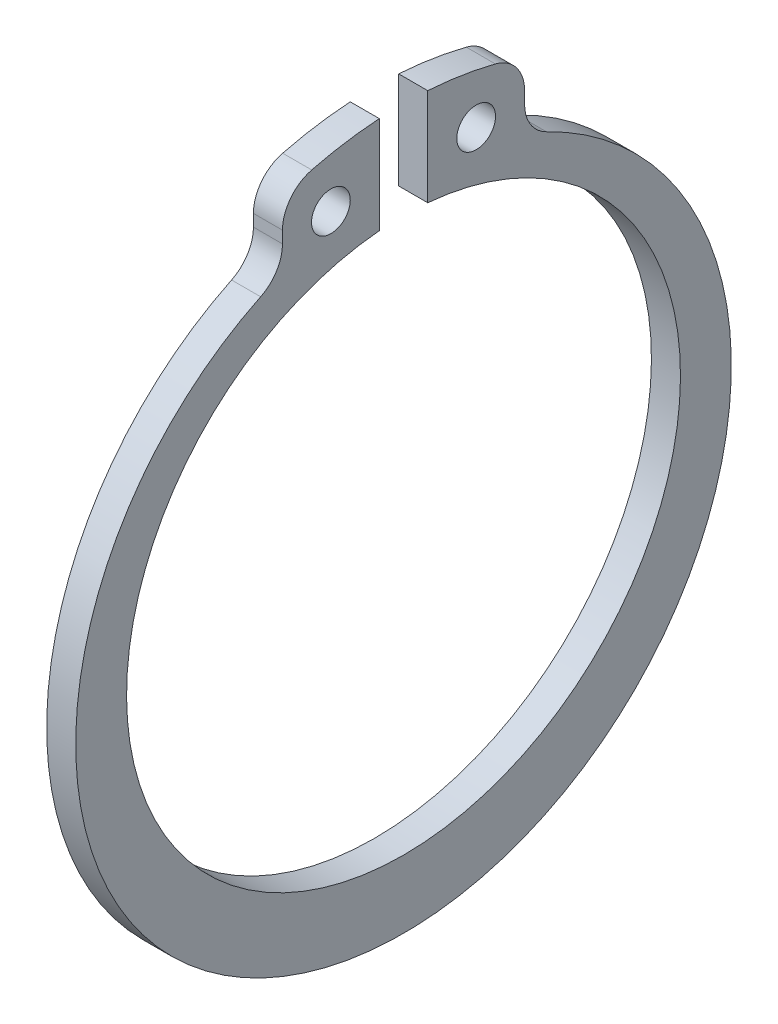
SolidWorks part; units mm, degrees
ref_plane "Front Plane" through (0, 0, 0) normal (0, 0, 1) x (1, 0, 0)
ref_plane "Top Plane" through (0, 0, 0) normal (0, 1, 0) x (1, 0, 0)
ref_plane "Right Plane" through (0, 0, 0) normal (1, 0, 0) x (0, 0, -1)
ref_plane "Plane1" through (0, 0, 0) normal (1, 0, 0) x (0, 0, -1)
sketch "Sketch1" plane through (0, 0, 0) normal (1, 0, 0) x (0, 0, -1)
  line L0 (6.25, 16.1571) -> (6.25, 16.7698)
  line L1 (1.25, 19.2595) -> (1.25, 14.2453)
  line L2 (-1.25, 14.2453) -> (-1.25, 19.2595)
  line L3 (-6.25, 16.7698) -> (-6.25, 16.1571)
  arc A0 (-7.3781, 14.3572) -> (7.3781, 14.3572) centre (0, -0.875) ccw
  arc A1 (7.3781, 14.3572) -> (6.25, 16.1571) centre (8.25, 16.1571) cw
  arc A2 (6.25, 16.7698) -> (4.7413, 18.7085) centre (4.25, 16.7698) ccw
  arc A3 (4.7413, 18.7085) -> (1.25, 19.2595) centre (0, 0) ccw
  arc A4 (1.25, 14.2453) -> (-1.25, 14.2453) centre (0, 0) cw
  arc A5 (-1.25, 19.2595) -> (-4.7413, 18.7085) centre (0, 0) ccw
  arc A6 (-4.7413, 18.7085) -> (-6.25, 16.7698) centre (-4.25, 16.7698) ccw
  arc A7 (-6.25, 16.1571) -> (-7.3781, 14.3572) centre (-8.25, 16.1571) cw
  circle A8 centre (3.75, 16.3659) radius 1
  circle A9 centre (-3.75, 16.3659) radius 1
extrude "Boss-Extrude1" add sketch "Sketch1" along normal blind 1.5
